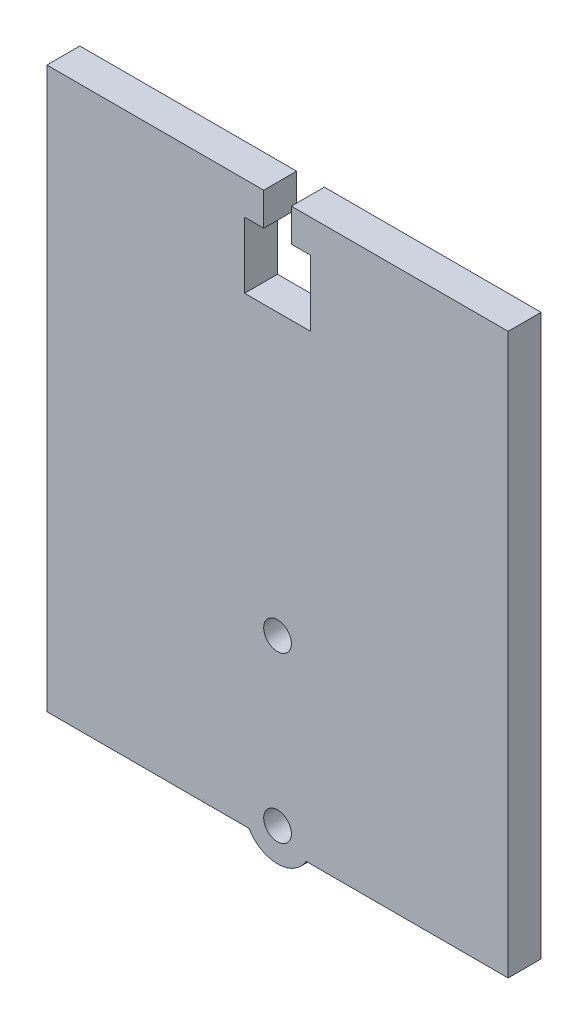
SolidWorks part; units mm, degrees
ref_plane "Front Plane" through (0, 0, 0) normal (0, 0, 1) x (1, 0, 0)
ref_plane "Top Plane" through (0, 0, 0) normal (0, 1, 0) x (1, 0, 0)
ref_plane "Right Plane" through (0, 0, 0) normal (1, 0, 0) x (0, 0, -1)
sketch "Sketch1" plane through (0, 0, 0) normal (0, 0, 1) x (1, 0, 0)
  line L1 (35, -42.5) -> (-35, -42.5)
  line L2 (35, -42.5) -> (35, 42.5)
  line L3 (35, 42.5) -> (-35, 42.5)
  line L4 (-35, -42.5) -> (-35, 42.5)
  line L5 (35, -42.5) -> (-35, 42.5) construction
  line L6 (35, 42.5) -> (-35, -42.5) construction
  point P0 (0, 0)
  dimension "D1" = 85
  dimension "D2" = 70
extrude "Boss-Extrude1" add sketch "Sketch1" along normal blind 5
sketch "Sketch2" plane through (0, 0, 5) normal (0, 0, 1) x (1, 0, 0)
  line L0 (0, 42.5) -> (0, 26.3631) construction
  line L1 (35, 42.5) -> (-35, 42.5) construction
  line L2 (2.1, 42.5) -> (2.1, 37.5)
  line L3 (2.1, 37.5) -> (5, 37.5)
  line L4 (5, 37.5) -> (5, 27.5)
  line L5 (5, 27.5) -> (-5, 27.5)
  line L6 (-5, 37.5) -> (-5, 27.5)
  line L7 (-2.1, 37.5) -> (-5, 37.5)
  line L8 (-2.1, 42.5) -> (-2.1, 37.5)
  line L9 (2.1, 42.5) -> (-2.1, 42.5)
  line L10 (-35, -15) -> (35, -15) construction
  line L11 (-35, 42.5) -> (-35, -42.5) construction
  line L12 (35, -42.5) -> (35, 42.5) construction
  line L13 (35, -40) -> (-35, -40) construction
  line L14 (30.0042, -17.5) -> (2.1, -17.5) construction
  line L15 (-50.5513, -37.5) -> (-2.1, -37.5) construction
  circle A0 centre (0, -15) radius 2.1
  circle A1 centre (0, -40) radius 2.1
  point P10 (3.55, 37.5)
  point P12 (0, 27.5)
  dimension "D7" = 4.2
  dimension "D8" = 4.2
  dimension "D1" = 2.1
  dimension "D2" = 5
  dimension "D3" = 10
  dimension "D4" = 5
  dimension "D5" = 2.5
  dimension "D6" = 2.5
extrude "Cut-Extrude1" cut sketch "Sketch2" against normal blind 5
sketch "Sketch3" plane through (0, 0, 5) normal (0, 0, 1) x (1, 0, 0)
  line L0 (-35, -42.5) -> (35, -42.5) construction
  line L1 (-4.3301, -42.5) -> (4.3301, -42.5)
  arc A0 (-4.3301, -42.5) -> (4.3301, -42.5) centre (0, -40) ccw
  dimension "D1" = 10
extrude "Boss-Extrude2" add sketch "Sketch3" against normal blind 5
